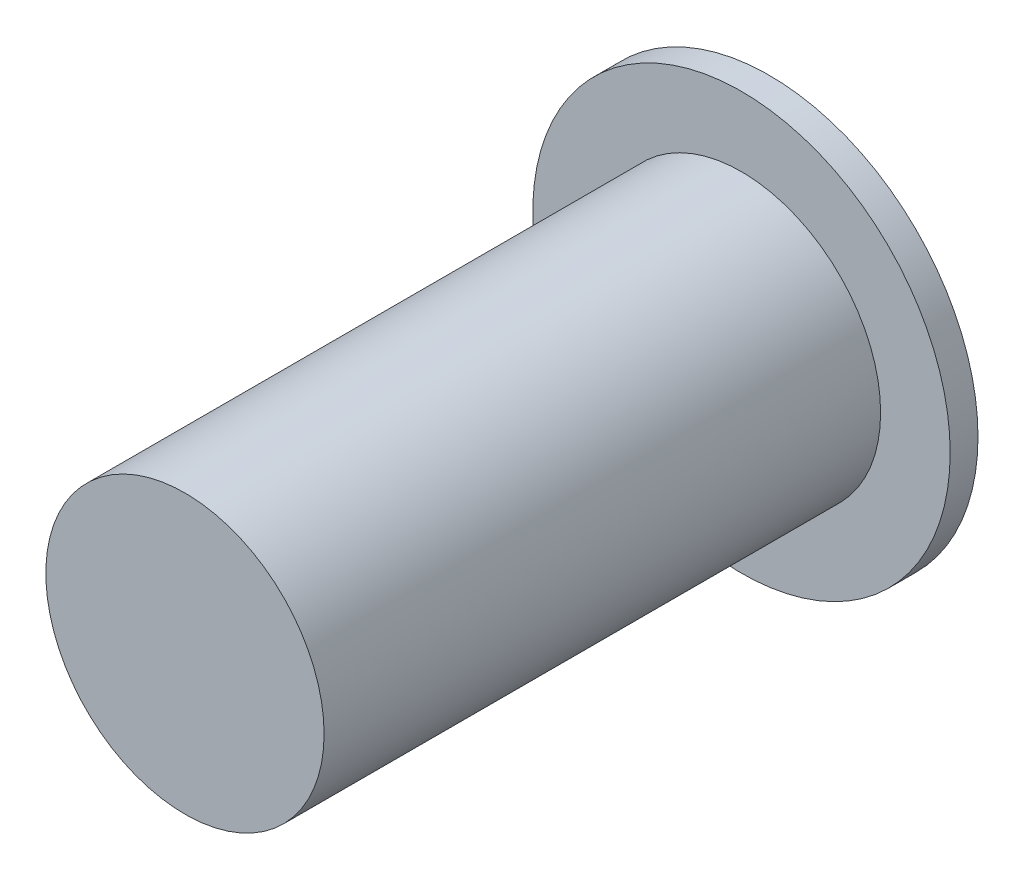
SolidWorks part; units mm, degrees
ref_plane "Alzado" through (0, 0, 0) normal (0, 0, 1) x (1, 0, 0)
ref_plane "Planta" through (0, 0, 0) normal (0, 1, 0) x (1, 0, 0)
ref_plane "Vista lateral" through (0, 0, 0) normal (1, 0, 0) x (0, 0, -1)
sketch "Croquis1" plane through (0, 0, 0) normal (0, 0, 1) x (1, 0, 0)
  circle A0 centre (0, 0) radius 0.75
  dimension "D1" = 1.5
extrude "Saliente-Extruir1" add sketch "Croquis1" along normal blind 0.1
sketch "Croquis2" plane through (0, 0, 0.1) normal (0, 0, 1) x (1, 0, 0)
  circle A0 centre (0, 0) radius 0.5
  dimension "D1" = 1
extrude "Saliente-Extruir2" add sketch "Croquis2" along normal blind 2
